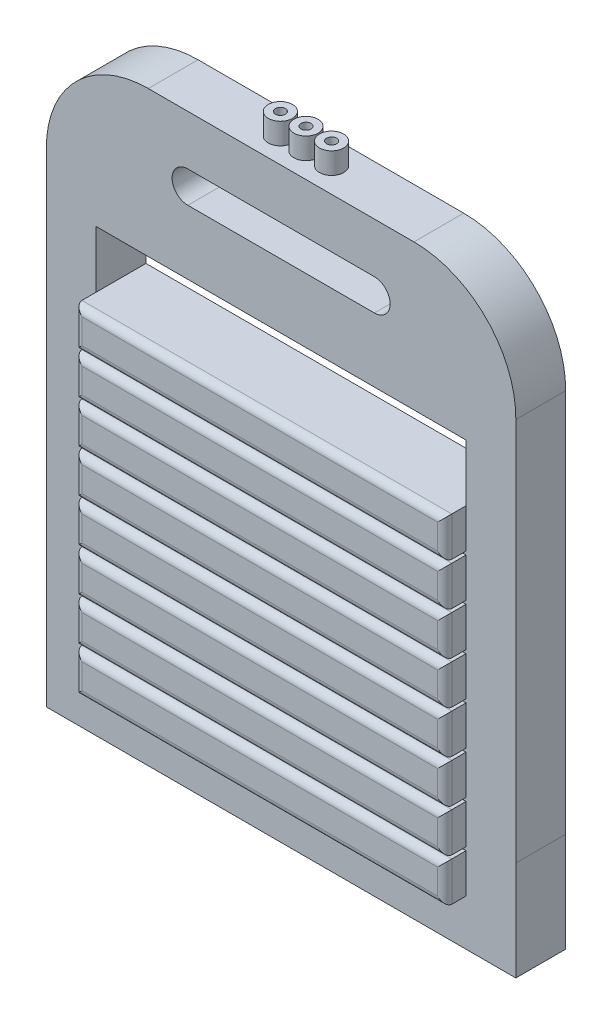
SolidWorks part; units mm, degrees
material "Cast Alloy Steel"
ref_plane "Front Plane" through (0, 0, 0) normal (0, 0, 1) x (1, 0, 0)
ref_plane "Top Plane" through (0, 0, 0) normal (0, 1, 0) x (1, 0, 0)
ref_plane "Right Plane" through (0, 0, 0) normal (1, 0, 0) x (0, 0, -1)
sketch "Sketch1" plane through (0, 0, 0) normal (0, 0, 1) x (1, 0, 0)
  line L1 (-330, 200) -> (330, 200)
  line L2 (-330, 200) -> (-330, -200)
  line L3 (-330, -200) -> (330, -200)
  line L4 (330, 200) -> (330, -200)
  line L5 (-330, 200) -> (330, -200) construction
  line L6 (-330, -200) -> (330, 200) construction
  point P0 (0, 0)
  dimension "D1" = 400
  dimension "D2" = 660
extrude "Boss-Extrude1" add sketch "Sketch1" along normal blind 70
sketch "Sketch2" plane through (0, 200, 0) normal (0, 1, 0) x (1, 0, 0)
  line L0 (330, -70) -> (-330, -70) construction
  line L1 (-330, 0) -> (-260, 0)
  line L2 (-330, 0) -> (-330, -70)
  line L3 (-330, -70) -> (-260, -70)
  line L4 (-260, 0) -> (-260, -70)
  line L5 (0, 0) -> (0, -70) construction
  line L6 (260, 0) -> (260, -70)
  line L7 (330, -70) -> (260, -70)
  line L8 (330, 0) -> (330, -70)
  line L9 (330, 0) -> (260, 0)
  dimension "D1" = 70
extrude "Boss-Extrude2" add sketch "Sketch2" along normal blind 140
sketch "Sketch3" plane through (330, 0, 0) normal (1, 0, 0) x (0, 0, -1)
  line L0 (0, -200) -> (0, 340) construction
  line L1 (-70, 340) -> (0, 340)
  line L2 (-70, 340) -> (-70, 280)
  line L3 (-70, 280) -> (0, 280)
  line L4 (0, 340) -> (0, 280)
  dimension "D1" = 60
extrude "Boss-Extrude3" add sketch "Sketch3" against normal up to surface (660 mm away) up to face at (-330, 70, 35)
sketch "Sketch4" plane through (0, 0, 70) normal (0, 0, 1) x (1, 0, 0)
  line L0 (0, 498.3613) -> (0, 454.0957) construction
  line L1 (-186.7321, 484.6184) -> (186.7321, 484.6184)
  line L2 (-131.1456, 392.3722) -> (131.1456, 392.3722) construction
  line L3 (-131.1456, 414.4805) -> (131.1456, 414.4805)
  line L4 (-131.1456, 370.2639) -> (131.1456, 370.2639)
  line L5 (-330, 340) -> (330, 340)
  arc A3 (-330, 340) -> (-186.7321, 484.6184) centre (-186.7321, 341.3442) cw
  arc A4 (330, 340) -> (186.7321, 484.6184) centre (186.7321, 341.3442) ccw
  arc A5 (-131.1456, 414.4805) -> (-131.1456, 370.2639) centre (-131.1456, 392.3722) ccw
  arc A6 (131.1456, 370.2639) -> (131.1456, 414.4805) centre (131.1456, 392.3722) ccw
  point P8 (0, 392.3722)
extrude "Boss-Extrude4" add sketch "Sketch4" against normal up to surface (70 mm away) up to face at (0, 240, 0)
sketch "Sketch5" plane through (0, 0, 70) normal (0, 0, 1) x (1, 0, 0)
  line L0 (-260, 200) -> (-260, -200) construction
  line L1 (-330, -200) -> (330, -200) construction
  line L2 (260, 200) -> (260, -200) construction
  line L4 (-260, 200) -> (260, 200)
  line L5 (-260, 200) -> (-260, 144.8057)
  line L6 (-260, 144.8057) -> (260, 144.8057)
  line L7 (260, 200) -> (260, 144.8057)
  line L8 (-260, 140) -> (-260, 84.8057)
  line L9 (-260, 140) -> (260, 140)
  line L10 (260, 140) -> (260, 84.8057)
  line L11 (-260, 84.8057) -> (260, 84.8057)
  line L13 (-260, 80) -> (-260, 24.8057)
  line L14 (-260, 80) -> (260, 80)
  line L15 (260, 80) -> (260, 24.8057)
  line L16 (-260, 24.8057) -> (260, 24.8057)
  line L18 (-260, 20) -> (-260, -35.1943)
  line L19 (-260, 20) -> (260, 20)
  line L20 (260, 20) -> (260, -35.1943)
  line L21 (-260, -35.1943) -> (260, -35.1943)
  line L23 (-260, -40) -> (-260, -95.1943)
  line L24 (-260, -40) -> (260, -40)
  line L25 (260, -40) -> (260, -95.1943)
  line L26 (-260, -95.1943) -> (260, -95.1943)
  line L28 (-260, -100) -> (-260, -155.1943)
  line L29 (-260, -100) -> (260, -100)
  line L30 (260, -100) -> (260, -155.1943)
  line L31 (-260, -155.1943) -> (260, -155.1943)
  line L37 (-260, -215.1943) -> (260, -215.1943) [skipped]
  line L38 (260, -160) -> (260, -215.1943) [skipped]
  line L39 (260, 140) -> (260, -260) construction
  line L40 (260, 80) -> (260, -320) construction
  line L41 (260, 20) -> (260, -380) construction
  line L42 (260, -40) -> (260, -440) construction
  line L43 (260, -100) -> (260, -500) construction
  line L44 (260, -160) -> (260, -560) construction
  line L45 (-260, -160) -> (-260, -215.1943) [skipped]
  line L46 (-260, -160) -> (260, -160) [skipped]
  dimension "D1" = 7
  dimension "D2" = 520
extrude "Boss-Extrude5" add sketch "Sketch5" along normal blind 30
fillet "Fillet1" radius 10 24 edges at (260, -127.5971, 100) (0, -155.1943, 100) (-260, -127.5971, 100) (0, -100, 100) (260, -67.5971, 100) (0, -95.1943, 100) (-260, -67.5971, 100) (0, -40, 100) (260, -7.5971, 100) (0, -35.1943, 100) (-260, -7.5971, 100) (0, 20, 100) (260, 52.4029, 100) (0, 24.8057, 100) (-260, 52.4029, 100) (0, 80, 100) (260, 112.4029, 100) (0, 84.8057, 100) (-260, 112.4029, 100) (0, 140, 100) (0, 200, 100) (260, 172.4029, 100) (0, 144.8057, 100) (-260, 172.4029, 100)
sketch "Sketch6" plane through (0, 484.6184, 0) normal (0, 1, 0) x (1, 0, 0)
  line L0 (-186.7321, -35) -> (186.7321, -35) construction
  line L1 (-186.7321, 0) -> (-186.7321, -70) construction
  line L2 (186.7321, 0) -> (186.7321, -70) construction
  circle A0 centre (-36, -35) radius 17
  circle A1 centre (0, -35) radius 17
  circle A2 centre (36, -35) radius 17
  circle A3 centre (-36, -35) radius 7
  circle A4 centre (0, -35) radius 7
  circle A5 centre (36, -35) radius 7
  dimension "D1" = 36
  dimension "D3" = 34
  dimension "D4" = 34
  dimension "D5" = 34
  dimension "D2" = 72
  dimension "D6" = 10
extrude "Boss-Extrude6" add sketch "Sketch6" along normal blind 30
sketch "Sketch9" plane through (0, 0, 70) normal (0, 0, 1) x (1, 0, 0)
  line L1 (-330, -200) -> (330.0004, -200)
  line L2 (-330, -200) -> (-330, -340)
  line L3 (-330, -340) -> (330.0004, -340)
  line L4 (330.0004, -200) -> (330.0004, -340)
  dimension "D1" = 140
extrude "Boss-Extrude7" add sketch "Sketch9" against normal blind 70
sketch "Sketch10" plane through (0, 0, 70) normal (0, 0, 1) x (1, 0, 0)
  line L0 (-260, -160) -> (260, -160)
  line L1 (-260, -100) -> (260, -100)
  line L2 (-260, -100) -> (-260, -155.1943)
  line L3 (-260, -155.1943) -> (260, -155.1943)
  line L4 (260, -100) -> (260, -155.1943)
  line L5 (-260, -160) -> (-260, -215.1943)
  line L6 (-260, -215.1943) -> (260, -215.1943)
  line L7 (260, -160) -> (260, -215.1943)
  line L8 (-260, -220) -> (260, -220)
  line L9 (-260, -220) -> (-260, -275.1943)
  line L10 (-260, -275.1943) -> (260, -275.1943)
  line L11 (260, -220) -> (260, -275.1943)
  dimension "D1" = 3
extrude "Boss-Extrude8" add sketch "Sketch10" along normal blind 30
fillet "Fillet2" radius 10 12 edges at (0, -220, 100) (260, -247.5971, 100) (0, -275.1943, 100) (-260, -247.5971, 100) (0, -160, 100) (260, -187.5971, 100) (0, -215.1943, 100) (-260, -187.5971, 100) (0, -100, 100) (260, -127.5971, 100) (0, -155.1943, 100) (-260, -127.5971, 100)
sketch "Sketch11" plane through (0, 514.6184, 0) normal (0, 1, 0) x (1, 0, 0)
  line L5 (-40.7658, -29.8729) -> (-31.2342, -29.8729)
  line L6 (-40.7658, -29.8729) -> (-40.7658, -40.1271)
  line L7 (-4.7658, -29.8729) -> (4.7658, -29.8729)
  line L8 (-4.7658, -29.8729) -> (-4.7658, -40.1271)
  line L9 (-4.7658, -40.1271) -> (4.7658, -40.1271)
  line L10 (4.7658, -29.8729) -> (4.7658, -40.1271)
  line L11 (-4.7658, -29.8729) -> (4.7658, -40.1271) construction
  line L12 (-4.7658, -40.1271) -> (4.7658, -29.8729) construction
  line L13 (31.2342, -29.8729) -> (40.7658, -29.8729)
  line L14 (31.2342, -29.8729) -> (31.2342, -40.1271)
  line L15 (31.2342, -40.1271) -> (40.7658, -40.1271)
  line L16 (40.7658, -29.8729) -> (40.7658, -40.1271)
  line L17 (31.2342, -29.8729) -> (40.7658, -40.1271) construction
  line L18 (31.2342, -40.1271) -> (40.7658, -29.8729) construction
  line L19 (-40.7658, -40.1271) -> (-31.2342, -40.1271)
  line L20 (-31.2342, -29.8729) -> (-31.2342, -40.1271)
  line L21 (-40.7658, -29.8729) -> (-31.2342, -40.1271) construction
  line L22 (-40.7658, -40.1271) -> (-31.2342, -29.8729) construction
  circle A0 centre (0, -35) radius 7 construction
  circle A1 centre (36, -35) radius 7 construction
  circle A2 centre (-36, -35) radius 7 construction
  point P0 (-36, -35)
  point P1 (-36, -35)
  point P5 (0, -35)
  point P14 (36, -35)
